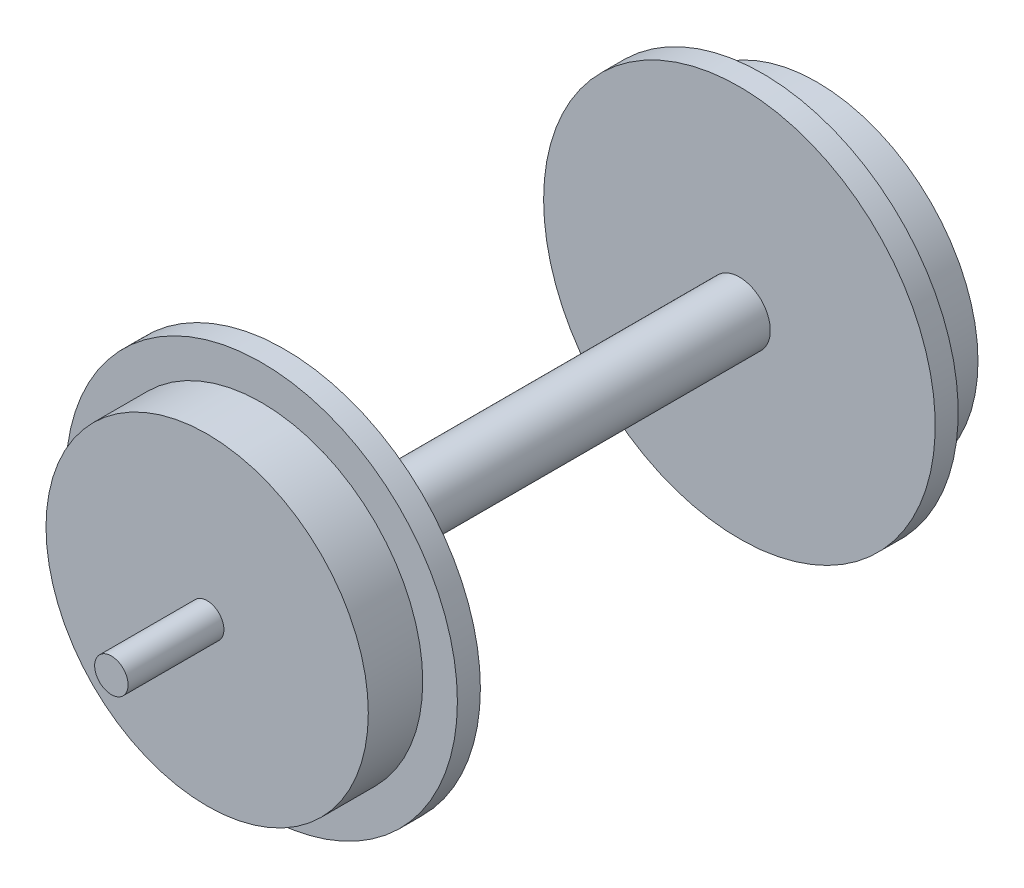
SolidWorks part; units mm, degrees
ref_plane "Front" through (0, 0, 0) normal (0, 0, 1) x (1, 0, 0)
ref_plane "Top" through (0, 0, 0) normal (0, 1, 0) x (1, 0, 0)
ref_plane "Right" through (0, 0, 0) normal (1, 0, 0) x (0, 0, -1)
sketch "Sketch1" plane through (0, 0, 0) normal (0, 0, 1) x (1, 0, 0)
  circle A0 centre (0, 0) radius 17.375
  dimension "D1" = 34.75
extrude "Boss-Extrude1" add sketch "Sketch1" along normal blind 2.04
sketch "Sketch2" plane through (0, 0, 2.04) normal (0, 0, 1) x (1, 0, 0)
  circle A0 centre (0, 0) radius 14.3
  dimension "D1" = 28.6
extrude "Boss-Extrude2" add sketch "Sketch2" along normal blind 4.83
sketch "Sketch3" plane through (0, 0, 0) normal (0, 0, -1) x (-1, 0, 0)
  circle A0 centre (0, 0) radius 2.74
  dimension "D1" = 5.48
extrude "Boss-Extrude3" add sketch "Sketch3" along normal blind 40.36
sketch "Sketch4" plane through (0, 0, -40.36) normal (0, 0, -1) x (-1, 0, 0)
  circle A0 centre (0, 0) radius 17.375
  dimension "D1" = 34.75
extrude "Boss-Extrude4" add sketch "Sketch4" along normal blind 2.04
sketch "Sketch5" plane through (0, 0, -42.4) normal (0, 0, -1) x (-1, 0, 0)
  circle A0 centre (0, 0) radius 14.3
  dimension "D1" = 28.6
extrude "Boss-Extrude5" add sketch "Sketch5" along normal blind 4.83
sketch "Sketch6" plane through (0, 0, -47.23) normal (0, 0, -1) x (-1, 0, 0)
  circle A0 centre (0, 0) radius 1.485
  dimension "D1" = 2.97
extrude "Boss-Extrude6" add sketch "Sketch6" along normal blind 8.5
sketch "Sketch7" plane through (0, 0, 6.87) normal (0, 0, 1) x (1, 0, 0)
  circle A0 centre (0, 0) radius 1.485
  dimension "D1" = 2.97
extrude "Boss-Extrude7" add sketch "Sketch7" along normal blind 8.5
